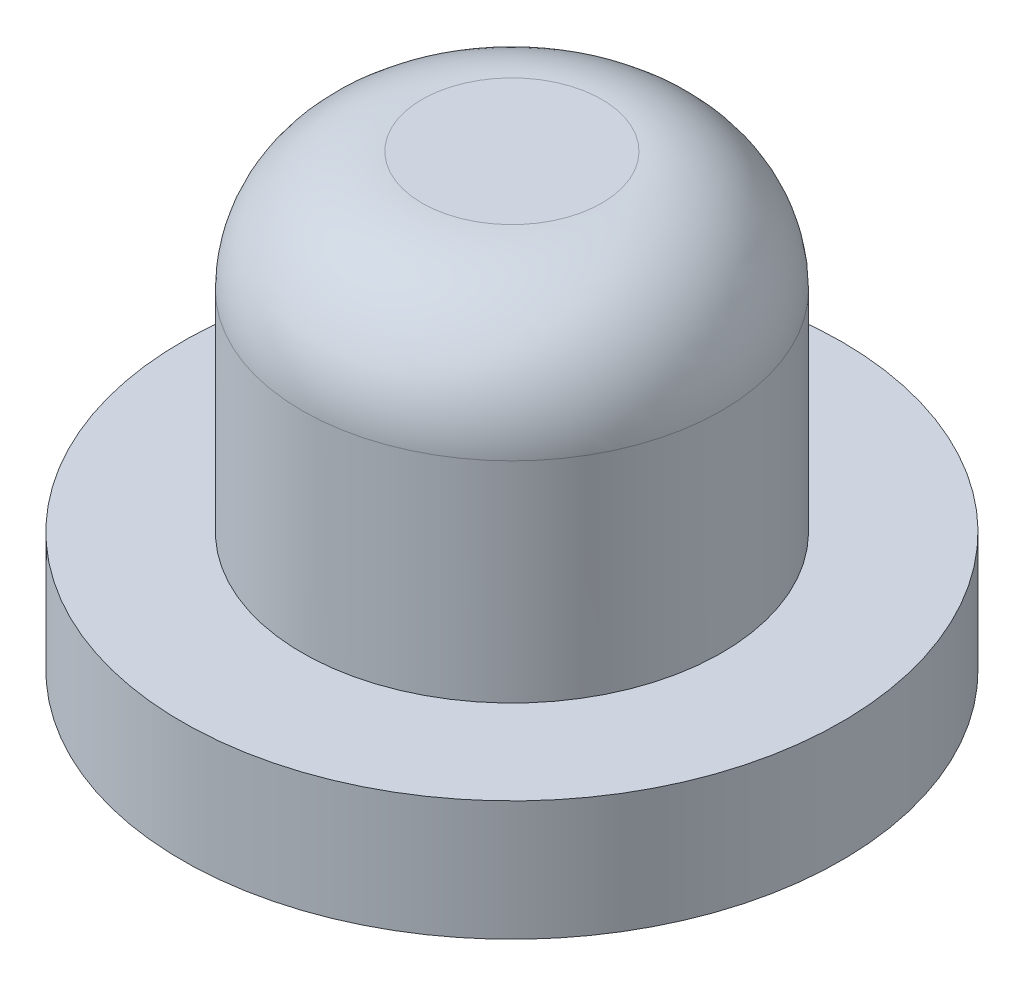
SolidWorks part; units mm, degrees
ref_plane "Ebene vorne" through (0, 0, 0) normal (0, 0, 1) x (1, 0, 0)
ref_plane "Ebene oben" through (0, 0, 0) normal (0, 1, 0) x (1, 0, 0)
ref_plane "Ebene rechts" through (0, 0, 0) normal (1, 0, 0) x (0, 0, -1)
sketch "Skizze1" plane through (0, 0, 0) normal (0, 1, 0) x (1, 0, 0)
  circle A0 centre (0, 0) radius 3.5
  dimension "D1" = 7
extrude "Aufsatz-Linear austragen1" add sketch "Skizze1" along normal blind 5.5
sketch "Skizze2" plane through (0, 0, 0) normal (0, -1, 0) x (1, 0, 0)
  circle A0 centre (0, 0) radius 5.5
  circle A1 centre (0, 0) radius 3.5 construction
  dimension "D1" = 2
extrude "Aufsatz-Linear austragen2" add sketch "Skizze2" along normal blind 2
sketch "Skizze3" plane through (0, -2, 0) normal (0, -1, 0) x (1, 0, 0)
  circle A0 centre (0, 0) radius 2
  dimension "D1" = 4
extrude "Schnitt-Linear austragen1" cut sketch "Skizze3" against normal blind 0.5 contours A0
fillet "Verrundung1" radius 2 1 edges at (0, 5.5, 3.5)
